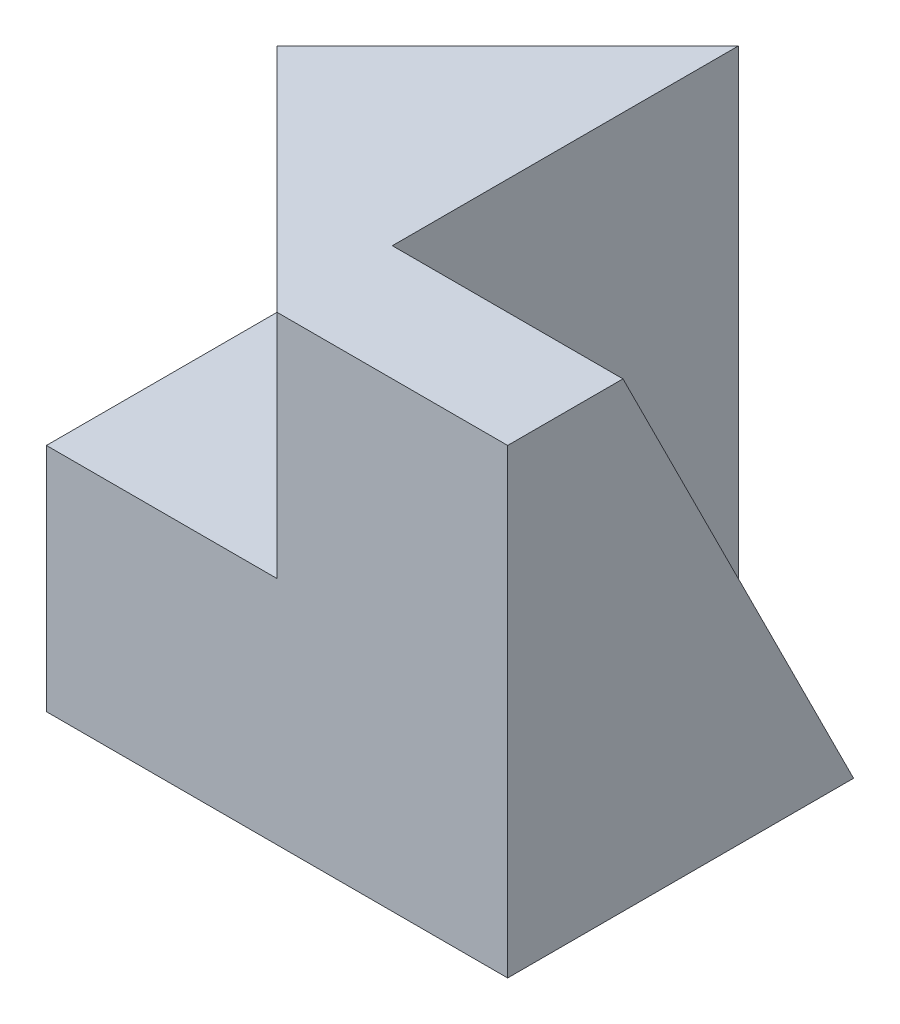
SolidWorks part; units mm, degrees
ref_plane "Front Plane" through (0, 0, 0) normal (0, 0, 1) x (1, 0, 0)
ref_plane "Top Plane" through (0, 0, 0) normal (0, 1, 0) x (1, 0, 0)
ref_plane "Right Plane" through (0, 0, 0) normal (1, 0, 0) x (0, 0, -1)
sketch "Sketch1" plane through (0, 0, 0) normal (0, 0, 1) x (1, 0, 0)
  line L0 (0, 20) -> (20, 20)
  line L1 (0, 0) -> (40, 0)
  line L2 (0, 0) -> (0, 40)
  line L3 (0, 40) -> (40, 40)
  line L4 (40, 0) -> (40, 40)
  line L5 (20, 20) -> (20, 40)
  dimension "D1" = 40
  dimension "D2" = 40
  dimension "D3" = 20
extrude "Boss-Extrude1" add sketch "Sketch1" along normal blind 40 contours L5 L0 L2 L1 L4 L3
sketch "Sketch2" plane through (20, 0, 0) normal (-1, 0, 0) x (0, 0, 1)
  line L0 (40, 20) -> (0, 20) construction
  line L1 (0, 40) -> (20, 40)
  line L2 (0, 40) -> (0, 20)
  line L3 (0, 20) -> (20, 20)
  line L4 (20, 40) -> (20, 20)
extrude "Boss-Extrude3" add sketch "Sketch2" along normal blind 20
sketch "Sketch3" plane through (40, 0, 0) normal (1, 0, 0) x (0, 0, -1)
  line L0 (-20, 40) -> (0, 0)
  line L1 (-40, 40) -> (0, 40) construction
  line L2 (0, 0) -> (0, 40)
  line L3 (0, 40) -> (-20, 40)
  line L4 (0, 0) -> (-30, 40)
  line L5 (-30, 40) -> (0, 40)
  line M1 (0, 0) -> (0, 40)
  line M2 (0, 40) -> (-40, 40)
  dimension "D1" = 30
extrude "Cut-Extrude2" cut sketch "Sketch3" against normal blind 20 contours L4 L0 M2 | L0 M2 M1
sketch "Sketch5" plane through (0, 0, 0) normal (0, -1, 0) x (-1, 0, 0)
  line L1 (-40, 0) -> (-20, 0)
  line L2 (-40, 0) -> (-40, -10)
  line L3 (-40, -10) -> (-20, -10)
  line L4 (-20, 0) -> (-20, -10)
  dimension "D1" = 20
  dimension "D2" = 10
extrude "Cut-Extrude3" cut sketch "Sketch5" against normal blind 20
sketch "Sketch6" plane through (0, 0, 0) normal (0, -1, 0) x (1, 0, 0)
  line L0 (20, 0) -> (0, 20)
  line L1 (0, 40) -> (0, 0) construction
  line L2 (0, 20) -> (0, 0)
  line L3 (0, 0) -> (20, 0)
extrude "Cut-Extrude4" cut sketch "Sketch6" against normal blind 52
sketch "Sketch7" plane through (40, 0, 0) normal (1, 0, 0) x (0, 0, -1)
  line L0 (-20, 0) -> (-30, 40)
  line L1 (-40, 0) -> (-10, 0) construction
  line L2 (-30, 40) -> (-10, 13.3333)
  line L3 (-10, 13.3333) -> (-10, 0)
  line L4 (-10, 0) -> (-20, 0)
  line L5 (-10, 0) -> (-30, 40)
  line M2 (-10, 0) -> (-10, 13.3333)
  line M3 (-10, 13.3333) -> (-30, 40)
  dimension "D1" = 10
extrude "Cut-Extrude8" cut sketch "Sketch7" against normal blind 20 contours L5 M2 M3
ref_plane "Plane1" through (-13.3333, 13.3333, 13.3333) normal (0.5774, -0.5774, -0.5774) x (-0.8165, -0.4082, -0.4082)
ref_plane "Plane2" through (-13.3333, 13.3333, 13.3333) normal (-0.5774, 0.5774, 0.5774) x (0.4082, -0.4082, 0.8165)
sketch "Sketch14" plane through (0, 40, 0) normal (0, 1, 0) x (1, 0, 0)
  line L0 (0, -20) -> (20, -40)
  line L1 (20, -40) -> (20, -20)
  line L2 (20, -20) -> (0, -20)
extrude "Boss-Extrude11" add sketch "Sketch14" against normal blind 20
